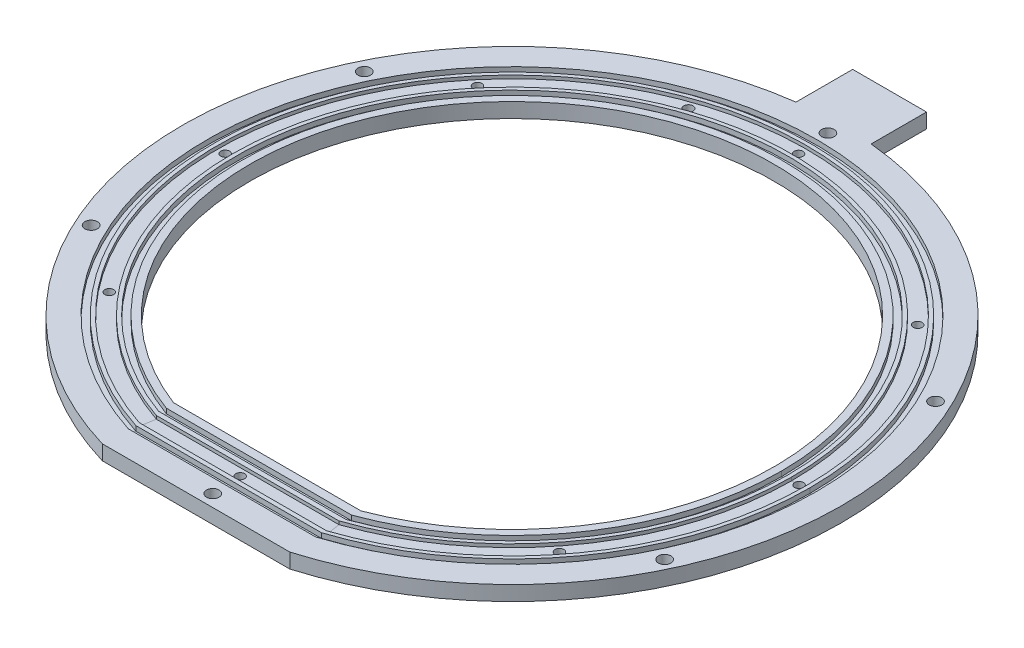
SolidWorks part; units mm, degrees
other "Markup1"
sketch "Sketch54" plane through (89.28, 3, -97.1935) normal (0.1341, 0.9493, -0.2845) x (0.9823, -0.1652, -0.0883)
material "Perspex (TM) GS Acrylic Cast Sheet"
ref_plane "Front Plane" through (0, 0, 0) normal (0, 0, 1) x (1, 0, 0)
ref_plane "Top Plane" through (0, 0, 0) normal (0, 1, 0) x (1, 0, 0)
ref_plane "Right Plane" through (0, 0, 0) normal (1, 0, 0) x (0, 0, -1)
sketch "Sketch1" plane through (0, 0, 0) normal (0, 1, 0) x (1, 0, 0)
  line L0 (8.406, 88.8834) -> (8.406, 103.8834)
  line L1 (8.406, 103.8834) -> (-11.594, 103.8834)
  line L2 (-11.594, 103.8834) -> (-11.594, 88.524)
  line L3 (-25.4, -85.5906) -> (25.4, -85.5906)
  arc A0 (25.4, -85.5906) -> (8.406, 88.8834) centre (0, 0) ccw
  arc A1 (-11.594, 88.524) -> (-25.4, -85.5906) centre (0, 0) ccw
  dimension "D1" = 178.56
extrude "Boss-Extrude2" add sketch "Sketch1" along normal blind 4 contours A0 L0 L1 L2 A1 L3
sketch "Sketch65" plane through (0, 4, 0) normal (0, 1, 0) x (1, 0, 0)
  line L1 (-25.4, -66.3011) -> (25.4, -66.3011)
  arc A0 (25.4, -66.3011) -> (-25.4, -66.3011) centre (0, 0) ccw
extrude "Cut-Extrude2" cut sketch "Sketch65" against normal blind 4
sketch "Sketch66" plane through (0, 4, 0) normal (0, 1, 0) x (1, 0, 0)
  line L1 (-25.4, -68.4386) -> (25.4, -68.4386)
  line L2 (-25.4, -70.3341) -> (25.4, -70.3341)
  arc A0 (25.4, -68.4386) -> (-25.4, -68.4386) centre (0, 0) ccw
  arc A1 (25.4, -70.3341) -> (-25.4, -70.3341) centre (0, 0) ccw
  dimension "D1" = 457.5873
  dimension "D2" = 468.8253
sketch "Sketch67" plane through (0, 0, 0) normal (0, 0, 1) x (1, 0, 0)
  line L0 (74.78, 4) -> (74.78, 2.665)
  line L1 (74.78, 4) -> (-74.78, 4) construction
  line L2 (74.78, 4) -> (73, 4)
  line L3 (73, 4) -> (-73, 4) construction
  line L4 (73, 4) -> (73, 2.665)
  line L5 (73, 2.665) -> (74.78, 2.665)
sweep "Cut-Sweep4" cut profiles "Sketch67" path "Sketch66"
sketch "Sketch70" plane through (0, 4, 0) normal (0, 1, 0) x (1, 0, 0)
  line L2 (-25.4, -76.6828) -> (25.4, -76.6828)
  line L3 (-25.4, -78.5557) -> (25.4, -78.5557)
  arc A2 (25.4, -76.6828) -> (-25.4, -76.6828) centre (0, 0) ccw
  arc A3 (25.4, -78.5557) -> (-25.4, -78.5557) centre (0, 0) ccw
  dimension "D1" = 506.679
  dimension "D2" = 517.9022
hole_wizard "M3 Clearance Hole1" positions "Sketch78" profile "Sketch79" hole size "M3" standard "ISO" end condition through all
sketch "Sketch78" plane through (0, 4, 0) normal (0, 1, 0) x (1, 0, 0)
  point P0 (0, 85.5799)
  point P2 (1.258, -82.3056)
  point P9 (1.258, -82.3056)
sketch "Sketch79" plane through (0, 4, -85.5799) normal (1, 0, 0) x (0, 0, 1)
  line L0 (0, 0) -> (0, 4)
  line L1 (0, 4) -> (1.7, 4)
  line L2 (1.7, 4) -> (1.7, 0)
  line L5 (1.7, 0) -> (0, 0)
  line L11 (0, -6.35) -> (0, 107.95) construction
  dimension "Thru Hole Dia." = 3.4
  dimension "Thru Hole Depth" = 4
hole_wizard "M3 Clearance Hole2" positions "Sketch80" profile "Sketch81" hole size "M3" standard "ISO" end condition through all
sketch "Sketch80" plane through (0, 4, 0) normal (0, 1, 0) x (1, 0, 0)
  point P0 (77.5173, 37.2138)
  point P2 (-77.2323, 37.2138)
  point P4 (77.9188, -36.5613)
  point P16 (77.5173, 37.2138)
sketch "Sketch81" plane through (77.5173, 4, -37.2138) normal (1, 0, 0) x (0, 0, 1)
  line L0 (0, 0) -> (0, 4)
  line L1 (0, 4) -> (1.7, 4)
  line L2 (1.7, 4) -> (1.7, 0)
  line L5 (1.7, 0) -> (0, 0)
  line L11 (0, -6.35) -> (0, 107.95) construction
  dimension "Thru Hole Dia." = 3.4
  dimension "Thru Hole Depth" = 4
hole_wizard "M3 Clearance Hole3" positions "Sketch82" profile "Sketch83" hole size "M3" standard "ISO" end condition through all
sketch "Sketch82" plane through (0, 4, 0) normal (0, 1, 0) x (1, 0, 0)
  point P0 (-78.1809, -35.8386)
  point P5 (-78.1809, -35.8386)
sketch "Sketch83" plane through (-78.1809, 4, 35.8386) normal (1, 0, 0) x (0, 0, 1)
  line L0 (0, 0) -> (0, 4)
  line L1 (0, 4) -> (1.7, 4)
  line L2 (1.7, 4) -> (1.7, 0)
  line L5 (1.7, 0) -> (0, 0)
  line L11 (0, -6.35) -> (0, 107.95) construction
  dimension "Thru Hole Dia." = 3.4
  dimension "Thru Hole Depth" = 4
sketch "Sketch85" plane through (0, 0, 0) normal (0, 1, 0) x (1, 0, 0)
  circle A0 centre (-25.5631, 73.3502) radius 1.25
  point P2 (-25.4386, 73.115)
  point P3 (-25.5631, 73.3502)
extrude "Cut-Extrude3" cut sketch "Sketch85" along normal blind 3.5
ref_plane "Plane2" through (-25.0865, 4, 68.5541) normal (-0.9391, 0, -0.3437) x (-0.3437, 0, 0.9391)
sketch "Sketch86" plane through (0, 4, 0) normal (0, 1, 0) x (1, 0, 0)
  line L1 (-25.4, -71.3964) -> (25.4, -71.3964)
  line L3 (-25.4, -75.6286) -> (25.4, -75.6286)
  arc A0 (25.4, -71.3964) -> (-25.4, -71.3964) centre (0, 0) ccw
  arc A3 (25.4, -75.6286) -> (-25.4, -75.6286) centre (0, 0) ccw
sketch "Sketch88" plane through (0, 0, 0) normal (0, 0, 1) x (1, 0, 0)
  line L0 (79.78, 4) -> (79.78, 3.11)
  line L1 (79.78, 4) -> (-79.78, 4) construction
  line L2 (75.78, 4) -> (75.78, 3.11)
  line L3 (75.78, 4) -> (-75.78, 4) construction
  line L4 (75.78, 3.11) -> (79.78, 3.11)
  line L5 (75.78, 4) -> (79.78, 4)
sweep "Cut-Sweep6" cut profiles "Sketch88" path "Sketch86"
sketch "Sketch89" plane through (0, 0, 0) normal (0, 0, 1) x (1, 0, 0)
  line L0 (82.56, 4) -> (82.56, 2.665)
  line L1 (82.56, 4) -> (-82.56, 4) construction
  line L2 (80.78, 4) -> (80.78, 2.665)
  line L3 (80.78, 4) -> (-80.78, 4) construction
  line L4 (80.78, 2.665) -> (82.56, 2.665)
  line L5 (80.78, 4) -> (82.56, 4)
sweep "Cut-Sweep7" cut profiles "Sketch89" path "Sketch70"
hole_wizard "M2 Clearance Hole1" positions "Sketch90" profile "Sketch91" hole size "M2" standard "ISO" end condition through all
sketch "Sketch90" plane through (0, 3.11, 0) normal (0, 1, 0) x (1, 0, 0)
  line L0 (75.78, 0) -> (79.78, 0) construction
  point P0 (0, 77.6318)
  point P2 (0, -73.6303)
  point P4 (77.78, 0)
  point P8 (-77.7041, 0)
  point P10 (56.2719, 53.6253)
  point P12 (-59.4017, 50.0554)
  point P14 (61.027, -48.1675)
  point P16 (-60.9323, -48.1675)
  point P19 (-60.9323, -48.1675)
sketch "Sketch91" plane through (0, 3.11, -77.6318) normal (1, 0, 0) x (0, 0, 1)
  line L0 (0, 0) -> (0, 3.11)
  line L1 (0, 3.11) -> (1.2, 3.11)
  line L2 (1.2, 3.11) -> (1.2, 0)
  line L5 (1.2, 0) -> (0, 0)
  line L11 (0, -6.35) -> (0, 107.95) construction
  dimension "Thru Hole Dia." = 2.4
  dimension "Thru Hole Depth" = 3.11
